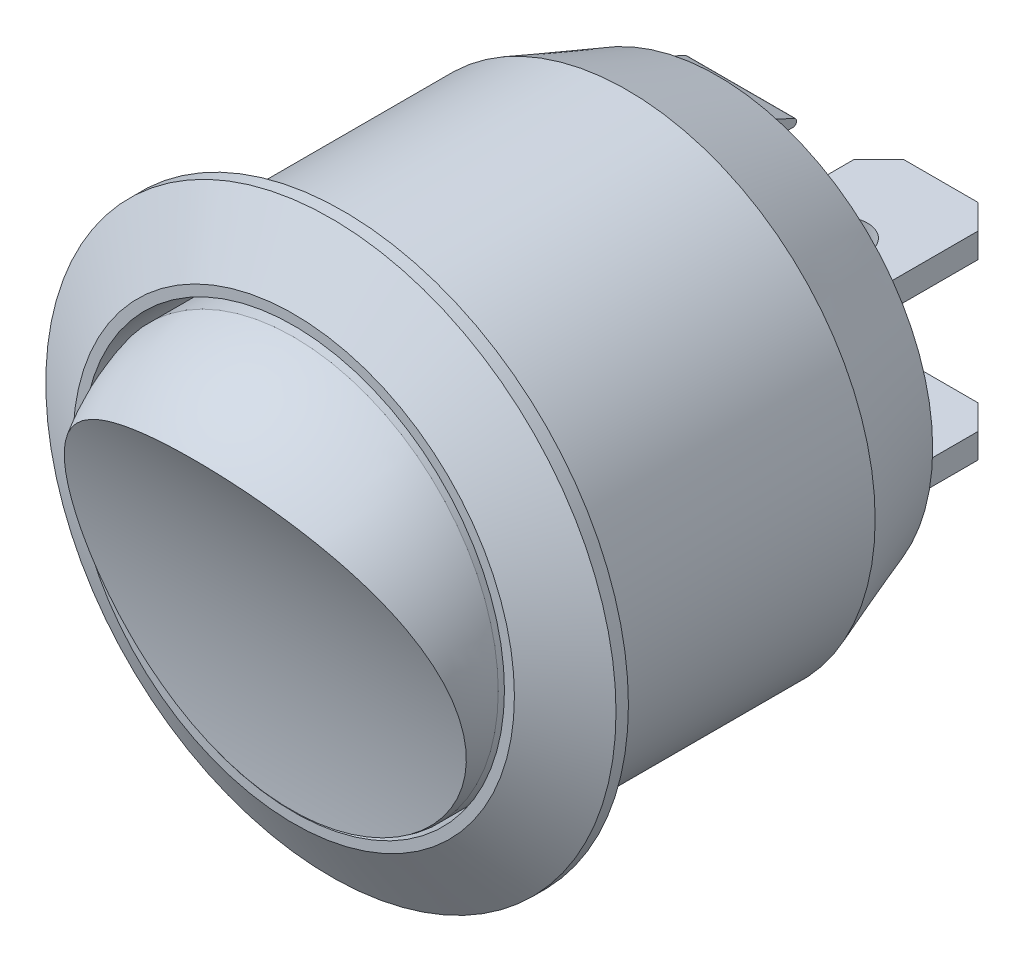
SolidWorks part; units mm, degrees
ref_plane "Front Plane" through (0, 0, 0) normal (0, 0, 1) x (1, 0, 0)
ref_plane "Top Plane" through (0, 0, 0) normal (0, 1, 0) x (1, 0, 0)
ref_plane "Right Plane" through (0, 0, 0) normal (1, 0, 0) x (0, 0, -1)
sketch "Sketch1" plane through (0, 0, 0) normal (0, 0, 1) x (1, 0, 0)
  circle A0 centre (0, 0) radius 10
  dimension "D1" = 20
extrude "Boss-Extrude1" add sketch "Sketch1" along normal blind 15
sketch "Sketch2" plane through (0, 0, 15) normal (0, 0, 1) x (1, 0, 0)
  circle A0 centre (0, 0) radius 11.5
  dimension "D1" = 23
extrude "Boss-Extrude2" add sketch "Sketch2" along normal blind 2
sketch "Sketch3" plane through (0, 0, 17) normal (0, 0, 1) x (1, 0, 0)
  circle A0 centre (0, 0) radius 8.5
  dimension "D1" = 17
extrude "Cut-Extrude1" cut sketch "Sketch3" against normal blind 2
sketch "Sketch4" plane through (0, 0, 15) normal (0, 0, 1) x (1, 0, 0)
  circle A0 centre (0, 0) radius 8.5
  circle A1 centre (0, 0) radius 8.5
  circle A2 centre (0, 0) radius 7
  circle M1 centre (0, 0) radius 8.5
  dimension "D1" = 14
extrude "Cut-Extrude2" cut sketch "Sketch4" against normal up to next contours A2 M1
sketch "Sketch5" plane through (0, 0, 0) normal (0, 0, -1) x (-1, 0, 0)
  line L1 (-2.5, -0.5) -> (2.5, -0.5)
  line L2 (-2.5, -0.5) -> (-2.5, 0.5)
  line L3 (-2.5, 0.5) -> (2.5, 0.5)
  line L4 (2.5, -0.5) -> (2.5, 0.5)
  line L5 (-2.5, -0.5) -> (2.5, 0.5) construction
  line L6 (-2.5, 0.5) -> (2.5, -0.5) construction
  line L7 (-2.5, 7.5) -> (2.5, 7.5)
  line L8 (-2.5, 7.5) -> (-2.5, 6.5)
  line L9 (-2.5, 6.5) -> (2.5, 6.5)
  line L10 (2.5, 7.5) -> (2.5, 6.5)
  line L11 (-2.5, 7.5) -> (2.5, 6.5) construction
  line L12 (-2.5, 6.5) -> (2.5, 7.5) construction
  circle A0 centre (0, 0) radius 10
  point P7 (0, 7)
  circle M1 centre (0, 0) radius 7
  dimension "D1" = 5
  dimension "D2" = 1
  dimension "D3" = 5
  dimension "D4" = 1
  dimension "D5" = 6
extrude "Boss-Extrude3" add sketch "Sketch5" against normal blind 1 and the other way blind 0.1 contours A0 M1 | L4 L1 L2 L3 L7 L10 L9 L8 M1
sketch "Sketch6" plane through (0, 0, -0.1) normal (0, 0, -1) x (-1, 0, 0)
  line L1 (-2.5, -7.5) -> (2.5, -7.5)
  line L2 (-2.5, -7.5) -> (-2.5, -6.5)
  line L3 (-2.5, -6.5) -> (2.5, -6.5)
  line L4 (2.5, -7.5) -> (2.5, -6.5)
  line L5 (-2.5, -7.5) -> (2.5, -6.5) construction
  line L6 (-2.5, -6.5) -> (2.5, -7.5) construction
  line L8 (-2.5, 0.5) -> (2.5, 0.5)
  line L9 (-2.5, 0.5) -> (-2.5, -0.5)
  line L10 (-2.5, -0.5) -> (2.5, -0.5)
  line L11 (2.5, 0.5) -> (2.5, -0.5)
  point P0 (0, -7)
  dimension "D2" = 1
  dimension "D3" = 5
extrude "Boss-Extrude4" add sketch "Sketch6" along normal blind 9
sketch "Sketch7" plane through (0, 0, 15) normal (0, 0, 1) x (1, 0, 0)
  circle A0 centre (0, -0.15) radius 8.25
  dimension "D1" = 16.5
  dimension "D2" = 0.15
extrude "Boss-Extrude5" add sketch "Sketch7" along normal blind 6
sketch "Sketch8" plane through (0, 0, 0) normal (1, 0, 0) x (0, 0, -1)
  line L0 (-21, -0.15) -> (-30.2169, -0.15) construction
  line L1 (-21, 8.1) -> (-21, -8.4) construction
  line L2 (-15, -10) -> (-15, 10) construction
  line L3 (-15, 8.1) -> (-21, 8.1) construction
  line L4 (-17, 11.5) -> (-17, -11.5) construction
  line L5 (-17, 8.1) -> (-21.7613, 8.1)
  line L6 (-21.7613, 8.1) -> (-21.7613, 5.7974)
  line L7 (-21.7613, 5.7974) -> (-21, 5.7974)
  arc A0 (-17, 8.1) -> (-21, 5.7974) centre (-15, 0) ccw
  dimension "D1" = 90
revolve "Cut-Revolve1" cut sketch "Sketch8" angle 360 about L0
sketch "Sketch9" plane through (0, 0, 0) normal (1, 0, 0) x (0, 0, -1)
  line L0 (-21, 5.7974) -> (-21, -8.3747)
  line L1 (-21, -8.3747) -> (-17.1, -8.3747)
  line L2 (-17, 8.1) -> (-17, -8.4) construction
  arc A0 (-21, 5.7974) -> (-17.1, -8.3747) centre (-44.6051, -8.3211) cw
  arc A1 (-21, -6.0974) -> (-17, -8.4) centre (-15, -0.3) ccw construction
  dimension "D1" = 0.1
extrude "Cut-Extrude3" cut sketch "Sketch9" against normal blind 16 and the other way blind 16
sketch "Sketch10" plane through (0, 0.5, 0) normal (0, 1, 0) x (1, 0, 0)
  line L0 (-2.5, 9.1) -> (2.5, 9.1) construction
  line L3 (0, 0.1) -> (0, 2.7094) construction
  circle A0 centre (0, 5.1) radius 1.05
  circle A1 centre (-2.5, 2.1) radius 0.4
  circle A2 centre (2.5, 2.1) radius 0.4
  dimension "D2" = 2.1
  dimension "D3" = 0.8
  dimension "D1" = 4
extrude "Cut-Extrude4" cut sketch "Sketch10" against normal through all
chamfer "Chamfer1" distance 1 angle 45 2 edges at (-2.5, 0, -9.1) (2.5, 0, -9.1)
chamfer "Chamfer2" distance 1 angle 45 2 edges at (-2.5, -7, -9.1) (2.5, -7, -9.1)
sketch "Sketch11" plane through (0, 0.5, 0) normal (0, 1, 0) x (1, 0, 0)
  line L0 (-3.6293, 1.2904) -> (-2.5, 0.3185)
  line L1 (-3.6293, 1.2904) -> (-3.9458, 1.4444)
  line L2 (-4.0762, 1.3046) -> (-3.3821, 0.1)
  line L4 (-3.3821, 0.1) -> (-2.5, 0.1)
  line L5 (0, 0) -> (0, 2.3345) construction
  line L6 (2.5, 0.3185) -> (2.5, 0.1)
  line L7 (3.3821, 0.1) -> (2.5, 0.1)
  line L8 (4.0762, 1.3046) -> (3.3821, 0.1)
  line L9 (3.6293, 1.2904) -> (3.9458, 1.4444)
  line L10 (-2.5, 1.7) -> (-2.5, 0.1) construction
  line L11 (-2.5, 0.3185) -> (-2.5, 0.1)
  line L12 (3.6293, 1.2904) -> (2.5, 0.3185)
  arc A0 (-4.0762, 1.3046) -> (-3.9458, 1.4444) centre (-3.9895, 1.3545) cw
  arc A1 (4.0762, 1.3046) -> (3.9458, 1.4444) centre (3.9895, 1.3545) ccw
  dimension "D1" = 0.1
extrude "Boss-Extrude8" add sketch "Sketch11" against normal blind 1
ref_plane "Plane1" through (0, -3.5, 0) normal (0, 1, 0) x (-1, 0, 0)
sketch "Sketch12" plane through (0, 0, 0) normal (1, 0, 0) x (0, 0, -1)
  line L0 (0.1, 0.55) -> (0.9355, 0.55)
  line L1 (0.1, -10) -> (0.1, 10) construction
  line L2 (0.9983, 0.8362) -> (0.1, 1.25)
  line L3 (0.1, 1.25) -> (0.1, 0.55)
  line L4 (8.1, 0.5) -> (2.5, 0.5) construction
  line L5 (0, 0) -> (3.7658, 0) construction
  line L6 (0.1, -1.25) -> (0.1, -0.55)
  line L7 (0.9983, -0.8362) -> (0.1, -1.25)
  line L8 (0.1, -0.55) -> (0.9355, -0.55)
  arc A0 (0.9355, 0.55) -> (0.9983, 0.8362) centre (0.9355, 0.7) ccw
  arc A1 (0.9355, -0.55) -> (0.9983, -0.8362) centre (0.9355, -0.7) cw
  dimension "D3" = 0.15
  dimension "D1" = 0.7
  dimension "D2" = 0.05
extrude "Boss-Extrude9" add sketch "Sketch12" along normal blind 2.2 and the other way blind 2.2
mirror "Mirror4" about plane through (0, -3.5, 0) normal (0, 1, 0) of "Boss-Extrude9", "Boss-Extrude8"
ref_plane "Plane2" through (0, 3.5, 0) normal (0, 1, 0) x (-1, 0, 0)
mirror "Mirror5" about plane through (0, 3.5, 0) normal (0, 1, 0) of "Boss-Extrude9"
sketch "Sketch13" plane through (0, 0, 0) normal (1, 0, 0) x (0, 0, -1)
  line L0 (1.7641, 8.0669) -> (-3.5472, 10)
  line L1 (-3.5472, 10) -> (0.1, 10)
  line L2 (1.7641, 8.0669) -> (1.7641, 10)
  line L3 (0, 0) -> (6.6072, 0) construction
  line L4 (1.7641, 10) -> (0.1, 10)
  line L5 (0.1, -10) -> (0.1, 10) construction
  dimension "D1" = 20
  dimension "D2" = 3.6472
revolve "Cut-Revolve2" cut sketch "Sketch13" angle 360 about L3
chamfer "Chamfer4" distance 1.5 angle 60 1 edges at (11.5, 0, 17)
